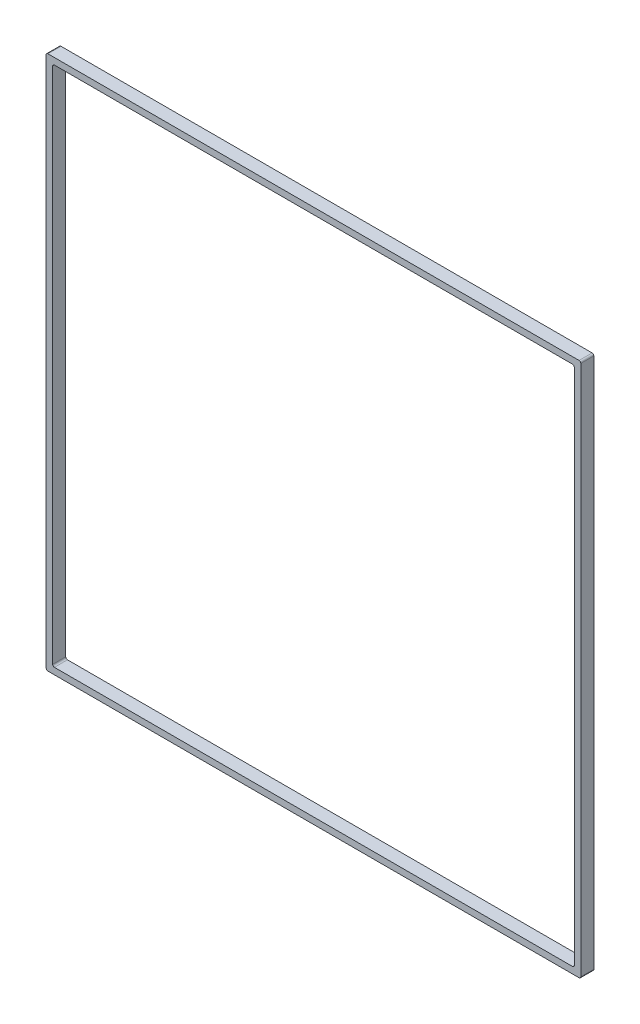
SolidWorks part; units mm, degrees
material "Copper"
ref_plane "Front Plane" through (0, 0, 0) normal (0, 0, 1) x (1, 0, 0)
ref_plane "Top Plane" through (0, 0, 0) normal (0, 1, 0) x (1, 0, 0)
ref_plane "Right Plane" through (0, 0, 0) normal (1, 0, 0) x (0, 0, -1)
sketch "Sketch1" plane through (0, 0, 0) normal (0, 0, 1) x (1, 0, 0)
  line L1 (-381, -381) -> (381, -381)
  line L2 (-381, -381) -> (-381, 381)
  line L3 (-381, 381) -> (381, 381)
  line L4 (381, -381) -> (381, 381)
  line L5 (-381, -381) -> (381, 381) construction
  line L6 (-381, 381) -> (381, -381) construction
  line L7 (-390.525, -390.525) -> (390.525, -390.525)
  line L8 (-390.525, -390.525) -> (-390.525, 390.525)
  line L9 (-390.525, 390.525) -> (390.525, 390.525)
  line L10 (390.525, -390.525) -> (390.525, 390.525)
  line L11 (-390.525, -390.525) -> (390.525, 390.525) construction
  line L12 (-390.525, 390.525) -> (390.525, -390.525) construction
  point P0 (0, 0)
  point P6 (0, 0)
  dimension "D1" = 762
  dimension "D2" = 762
  dimension "D3" = 781.05
  dimension "D4" = 781.05
extrude "Boss-Extrude1" add sketch "Sketch1" along normal blind 19.05
fillet "Fillet1" radius 2.54 8 edges at (381, 381, 9.525) (381, -381, 9.525) (-381, -381, 9.525) (-381, 381, 9.525) (390.525, -390.525, 9.525) (-390.525, -390.525, 9.525) (-390.525, 390.525, 9.525) (390.525, 390.525, 9.525)
sketch "Sketch2" plane through (0, 0, 0) normal (0, 0, -1) x (-1, 0, 0)
  circle A0 centre (0, 0) radius 355.6
